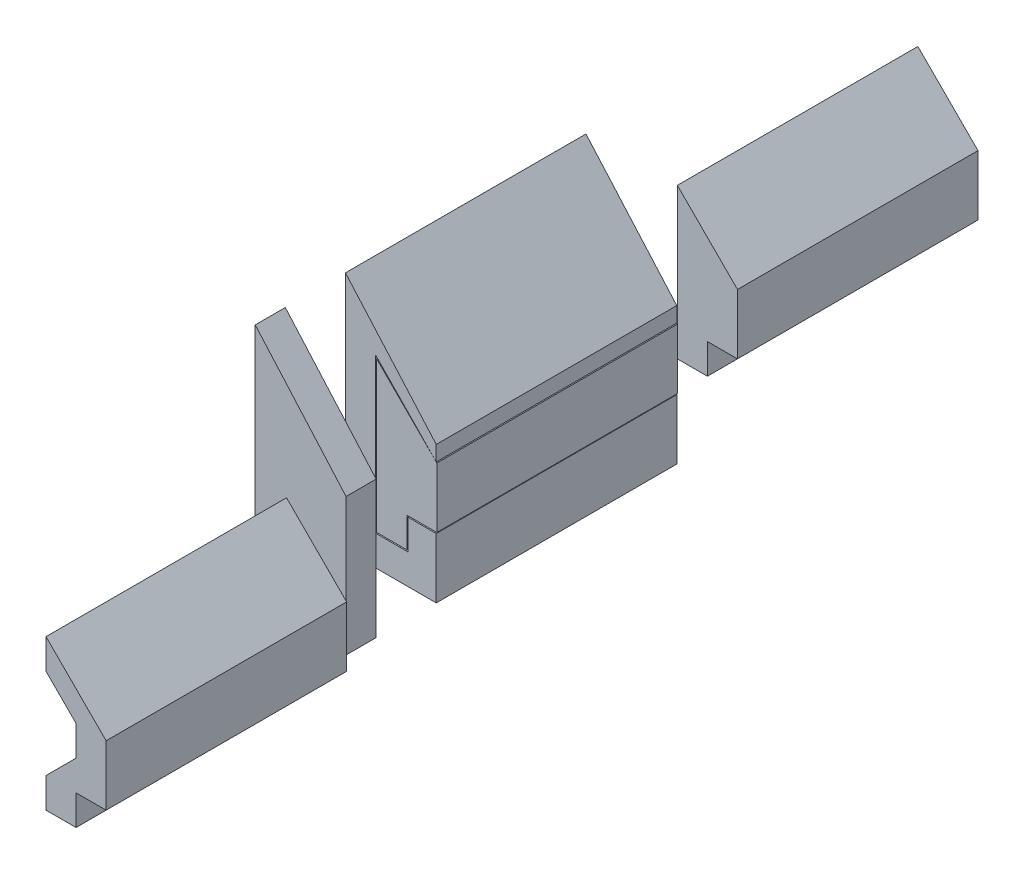
SolidWorks part; units mm, degrees
ref_plane "Front Plane" through (0, 0, 0) normal (0, 0, 1) x (1, 0, 0)
ref_plane "Top Plane" through (0, 0, 0) normal (0, 1, 0) x (1, 0, 0)
ref_plane "Right Plane" through (0, 0, 0) normal (1, 0, 0) x (0, 0, -1)
sketch "male_FULL" plane through (0, 0, 0) normal (0, 0, 1) x (1, 0, 0)
  line L0 (0, 0) -> (0, 10)
  line L1 (0, 10) -> (-10, 20)
  line L2 (-10, 20) -> (-10, -5)
  line L3 (-10, -5) -> (-5, -5)
  line L4 (-5, -5) -> (-5, 0)
  line L5 (-5, 0) -> (0, 0)
  line L6 (-5, 0) -> (-16.5356, 0) construction
  line L7 (0, 10) -> (-18.3231, 10) construction
  point P3 (-10, 10)
  dimension "D1" = 10
  dimension "D2" = 5
  dimension "D3" = 5
  dimension "D4" = 5
  dimension "D5" = 10
sketch "female" plane through (0, 0, 0) normal (0, 0, 1) x (1, 0, 0)
  line L0 (0, 0) -> (0, -20.2389) construction
  line L1 (0, 0) -> (0, 19.4218) construction
  line L2 (0, 10) -> (0, 12.5) construction
  line L3 (-5, 0) -> (0, 0) construction
  line L4 (-0.1, -0.2) -> (-0.1, -10.2)
  line L5 (-0.1, 12.6319) -> (-15.2, 29.8)
  line L6 (-15.2, 29.8) -> (-15.2, -10.2)
  line L7 (-15.2, -10.2) -> (-0.1, -10.2)
  line L8 (0, 10) -> (-0.1, 10) construction
  line L9 (0, 10) -> (-18.3231, 10) construction
  line L10 (-0.1, 10.1028) -> (-10.2, 20.4828)
  line L11 (-10.2, 20.4828) -> (-10.2, -5.2)
  line L12 (-10.2, -5.2) -> (-4.8, -5.2)
  line L13 (-4.8, -5.2) -> (-4.8, -0.2)
  line L14 (-4.8, -0.2) -> (-0.1, -0.2)
  line L15 (0, 0) -> (0, -0.6818) construction
  line L16 (-5, 0) -> (-16.5356, 0) construction
  line L17 (-0.1, 10.1028) -> (-0.1, 12.6319)
  line L18 (-0.1, 10.1028) -> (0, 10.1028)
  dimension "D2" = 0.1
  dimension "D3" = 0.2
  dimension "D4" = 5.4
  dimension "D5" = 25.6828
  dimension "D6" = 40
  dimension "D1" = 2.5
  dimension "D7" = 5
  dimension "D8" = 15.1
  dimension "D9" = 4.7
  dimension "D10" = 5
  dimension "D11" = 0.1
  dimension "D12" = 0.1028
  dimension "D13" = 2.6319
  dimension "D14" = 0.1
sketch "male_lite" plane through (0, 0, 0) normal (0, 0, 1) x (1, 0, 0)
  line L0 (0, 10) -> (-10, 20) construction
  line L1 (-10, 20) -> (-10, -5) construction
  line L2 (-5, -5) -> (-5, 0) construction
  line L3 (-5, 0) -> (0, 0) construction
  line L4 (-10, -5) -> (-5, -5) construction
  line L5 (0, 10) -> (-10, 20)
  line L6 (-10, 20) -> (-10, 15)
  line L7 (-5, -5) -> (-5, 0)
  line L8 (-5, 0) -> (0, 0)
  line L9 (-10, -5) -> (-5, -5)
  line L10 (-10, 20) -> (-10, 15) construction
  line L11 (0, 10) -> (-5, 10) construction
  line L12 (0, 10) -> (-18.3231, 10) construction
  line L13 (-10, 15) -> (-5, 10)
  line L14 (-5, 0) -> (-5, 5) construction
  line L15 (-5, 10) -> (-5, 5)
  line L16 (-5, 5) -> (-10, 0)
  line L17 (-5, 0) -> (-16.5356, 0) construction
  line L18 (-10, 0) -> (-10, -5)
  line L19 (0, 10) -> (0, 0)
  dimension "D1" = 5
  dimension "D2" = 5
  dimension "D3" = 5
  dimension "D4" = 5
extrude "Boss-Extrude2" add sketch "female" along normal blind 40 contours L17 L5 L6 L7 L4 L14 L13 L12 L11 L10
extrude "Boss-Extrude3" add sketch "male_FULL" along normal blind 40 separate body
ref_plane "plane_stop" through (0, 0, 50) normal (0, 0, 1) x (1, 0, 0)
sketch "female_stop" plane through (0, 0, 50) normal (0, 0, 1) x (1, 0, 0)
  line L0 (-0.1, -0.2) -> (-0.1, 10.1028)
  line L10 (-10.2, 20.4828) -> (-0.1, 10.1028)
  line L11 (-0.1, 10.1028) -> (-0.1, 12.6319)
  line L12 (-0.1, 12.6319) -> (-15.2, 29.8)
  line L13 (-15.2, 29.8) -> (-15.2, -10.2)
  line L14 (-15.2, -10.2) -> (-0.1, -10.2)
  line L15 (-0.1, -10.2) -> (-0.1, -0.2)
  line L16 (-0.1, -0.2) -> (-4.8, -0.2)
  line L17 (-4.8, -0.2) -> (-4.8, -5.2)
  line L18 (-4.8, -5.2) -> (-10.2, -5.2)
  line L19 (-10.2, -5.2) -> (-10.2, 20.4828)
  line L21 (-0.1, 10.1028) -> (-0.1, 12.6319)
  line L22 (-0.1, 12.6319) -> (-15.2, 29.8)
  line L23 (-15.2, 29.8) -> (-15.2, -10.2)
  line L24 (-15.2, -10.2) -> (-0.1, -10.2)
  line L25 (-0.1, -10.2) -> (-0.1, -0.2)
  dimension "D1" = 0
extrude "Boss-Extrude4" add sketch "female_stop" along normal blind 5 separate body
ref_plane "Plane2" through (0, 0, 60) normal (0, 0, 1) x (1, 0, 0)
sketch "Sketch6" plane through (0, 0, 60) normal (0, 0, 1) x (1, 0, 0)
  line L0 (5, 2.5) -> (-5, 12.5)
  line L1 (-5, 12.5) -> (-5, 7.5)
  line L2 (0, -12.5) -> (0, -7.5)
  line L3 (0, -7.5) -> (5, -7.5)
  line L4 (-5, -12.5) -> (0, -12.5)
  line L5 (-5, 12.5) -> (-5, 7.5) construction
  line L6 (5, 2.5) -> (0, 2.5) construction
  line L7 (-5, 7.5) -> (0, 2.5)
  line L8 (0, -7.5) -> (0, -2.5) construction
  line L9 (0, 2.5) -> (0, -2.5)
  line L10 (0, -2.5) -> (-5, -7.5)
  line L11 (-5, -7.5) -> (-5, -12.5)
  line L12 (5, 2.5) -> (5, -7.5)
extrude "Boss-Extrude6" add sketch "Sketch6" along normal blind 40 separate body
ref_plane "Plane3" through (0, 0, -10) normal (0, 0, -1) x (-1, 0, 0)
sketch "Sketch7" plane through (0, 0, -10) normal (0, 0, -1) x (-1, 0, 0)
  line L0 (0, 0) -> (0, 10)
  line L7 (18.3231, 10) -> (-18.3231, 10) construction
  line L8 (0, 10) -> (0, 49.0743) construction
  line L9 (5, 0) -> (14.9277, 0) construction
  line L10 (5, -5) -> (5, 0)
  line L11 (10, -5) -> (5, -5)
  line L12 (10, 20) -> (10, -5)
  line L13 (0, 10) -> (10, 20)
  line L14 (0, 0) -> (0, -15.0939) construction
  line L15 (0, 0) -> (0, -20.2389) construction
  line L17 (5, 0) -> (0, 0)
  point P18 (10, 10)
  dimension "D1" = 10
  dimension "D2" = 5
  dimension "D3" = 5
  dimension "D4" = 5
  dimension "D5" = 25
extrude "Boss-Extrude7" add sketch "Sketch7" along normal blind 40 separate body contours L11 L10 L17 L0 L13 L12
